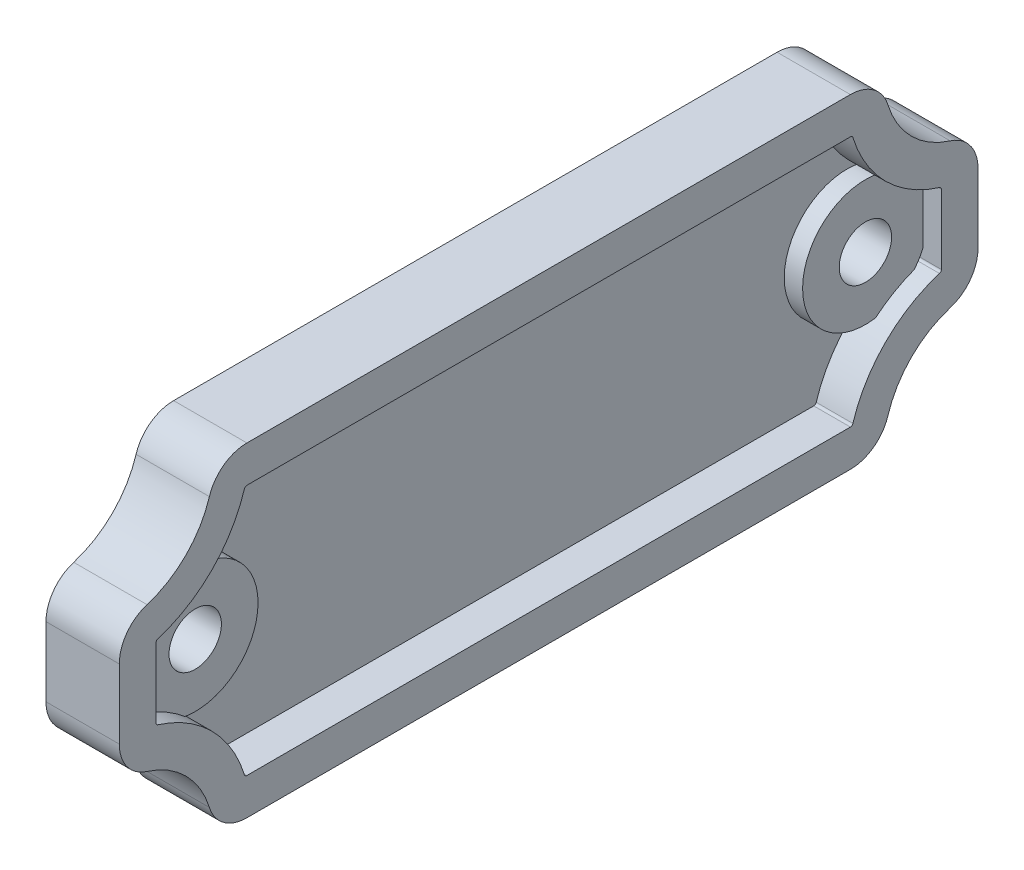
SolidWorks part; units mm, degrees
material "Brass"
ref_plane "Front Plane" through (0, 0, 0) normal (0, 0, 1) x (1, 0, 0)
ref_plane "Top Plane" through (0, 0, 0) normal (0, 1, 0) x (1, 0, 0)
ref_plane "Right Plane" through (0, 0, 0) normal (1, 0, 0) x (0, 0, -1)
sketch "Sketch1" plane through (0, 0, 0) normal (1, 0, 0) x (0, 0, -1)
  line L0 (0, 0) -> (43678.9312, 0) construction
  line L1 (0, 0) -> (0, 43678.9312) construction
  line L2 (-32, 0) -> (-32, 43678.9312) construction
  line L3 (-41, -1031) -> (-41, -15.5) construction
  line L4 (32, 0) -> (32, 43678.9312) construction
  line L5 (41, -1000) -> (41, -15.5) construction
  line L6 (41, 15.5) -> (41, 43678.9312) construction
  line L7 (28.8139, -15.5) -> (-28.8139, -15.5)
  line L8 (41, -3.3139) -> (41, 3.3139)
  line L9 (28.8139, 15.5) -> (-28.8139, 15.5)
  line L10 (-41, -3.3139) -> (-41, 3.3139)
  line L11 (41, -15.5) -> (-41, 15.5) construction
  line L12 (41, 15.5) -> (-41, -15.5) construction
  line L13 (41, -6.5) -> (41, 6.5) construction
  line L14 (-41, -6.5) -> (-41, 6.5) construction
  line L15 (-41, 15.5) -> (-41, 43678.9312) construction
  arc A0 (-32.3981, 12.8529) -> (-38.3529, 6.8981) centre (-41, 15.5) cw
  arc A1 (-32.3981, -12.8529) -> (-38.3529, -6.8981) centre (-41, -15.5) ccw
  arc A2 (32.3981, -12.8529) -> (38.3529, -6.8981) centre (41, -15.5) cw
  arc A3 (32.3981, 12.8529) -> (38.3529, 6.8981) centre (41, 15.5) ccw
  arc A4 (32.3981, 12.8529) -> (28.8139, 15.5) centre (28.8139, 11.75) ccw
  arc A5 (41, 3.3139) -> (38.3529, 6.8981) centre (37.25, 3.3139) ccw
  arc A6 (41, -3.3139) -> (38.3529, -6.8981) centre (37.25, -3.3139) cw
  arc A7 (28.8139, -15.5) -> (32.3981, -12.8529) centre (28.8139, -11.75) ccw
  arc A8 (-32.3981, -12.8529) -> (-28.8139, -15.5) centre (-28.8139, -11.75) ccw
  arc A9 (-38.3529, -6.8981) -> (-41, -3.3139) centre (-37.25, -3.3139) cw
  arc A10 (-41, 3.3139) -> (-38.3529, 6.8981) centre (-37.25, 3.3139) cw
  arc A11 (-32.3981, 12.8529) -> (-28.8139, 15.5) centre (-28.8139, 11.75) cw
  circle A12 centre (-32, 0) radius 2.5
  circle A13 centre (32, 0) radius 2.5
  point P13 (0, 0)
  point P28 (32, 15.5)
  point P37 (32, -15.5)
  point P40 (-32, -15.5)
  point P49 (-32, 15.5)
  dimension "D4" = 9
  dimension "D5" = 3.75
  dimension "D6" = 5
  dimension "D1" = 9
  dimension "D2" = 82
  dimension "D3" = 31
extrude "Boss-Extrude1" add sketch "Sketch1" along normal blind 7
sketch "Sketch6" plane through (7, 0, 0) normal (1, 0, 0) x (0, 0, -1)
  line L8 (28.8139, 12) -> (-28.8139, 12)
  line L9 (-37.5, 3.3139) -> (-37.5, -3.3139)
  line L10 (-28.8139, -12) -> (28.8139, -12)
  line L11 (37.5, -3.3139) -> (37.5, 3.3139)
  line L12 (28.8139, 12) -> (-28.8139, 12)
  line L13 (-37.5, 3.3139) -> (-37.5, -3.3139)
  line L14 (-28.8139, -12) -> (28.8139, -12)
  line L15 (37.5, -3.3139) -> (37.5, 3.3139)
  arc A12 (29.0529, 11.8235) -> (28.8139, 12) centre (28.8139, 11.75) ccw
  arc A13 (29.0529, 11.8235) -> (28.8139, 12) centre (28.8139, 11.75) ccw
  arc A14 (-28.8139, 12) -> (-29.0529, 11.8235) centre (-28.8139, 11.75) ccw
  arc A15 (-28.8139, 12) -> (-29.0529, 11.8235) centre (-28.8139, 11.75) ccw
  arc A16 (-37.3235, 3.5529) -> (-37.5, 3.3139) centre (-37.25, 3.3139) ccw
  arc A17 (-37.3235, 3.5529) -> (-37.5, 3.3139) centre (-37.25, 3.3139) ccw
  arc A18 (-37.5, -3.3139) -> (-37.3235, -3.5529) centre (-37.25, -3.3139) ccw
  arc A19 (-37.5, -3.3139) -> (-37.3235, -3.5529) centre (-37.25, -3.3139) ccw
  arc A20 (-29.0529, -11.8235) -> (-28.8139, -12) centre (-28.8139, -11.75) ccw
  arc A21 (-29.0529, -11.8235) -> (-28.8139, -12) centre (-28.8139, -11.75) ccw
  arc A22 (28.8139, -12) -> (29.0529, -11.8235) centre (28.8139, -11.75) ccw
  arc A23 (28.8139, -12) -> (29.0529, -11.8235) centre (28.8139, -11.75) ccw
  arc A24 (-37.3235, 3.5529) -> (-29.0529, 11.8235) centre (-41, 15.5) ccw
  arc A25 (-29.0529, -11.8235) -> (-37.3235, -3.5529) centre (-41, -15.5) ccw
  arc A26 (37.3235, -3.5529) -> (29.0529, -11.8235) centre (41, -15.5) ccw
  arc A27 (29.0529, 11.8235) -> (37.3235, 3.5529) centre (41, 15.5) ccw
  arc A28 (-37.3235, 3.5529) -> (-29.0529, 11.8235) centre (-41, 15.5) ccw
  arc A29 (-29.0529, -11.8235) -> (-37.3235, -3.5529) centre (-41, -15.5) ccw
  arc A30 (37.3235, -3.5529) -> (29.0529, -11.8235) centre (41, -15.5) ccw
  arc A31 (29.0529, 11.8235) -> (37.3235, 3.5529) centre (41, 15.5) ccw
  arc A32 (37.3235, -3.5529) -> (37.5, -3.3139) centre (37.25, -3.3139) ccw
  arc A33 (37.3235, -3.5529) -> (37.5, -3.3139) centre (37.25, -3.3139) ccw
  arc A34 (37.5, 3.3139) -> (37.3235, 3.5529) centre (37.25, 3.3139) ccw
  arc A35 (37.5, 3.3139) -> (37.3235, 3.5529) centre (37.25, 3.3139) ccw
  dimension "A" = 3.5
extrude "Cut-Extrude1" cut sketch "Sketch6" against normal blind 3.5
sketch "Sketch7" plane through (3.5, 0, 0) normal (1, 0, 0) x (0, 0, -1)
  circle A0 centre (32, 0) radius 6
  circle A1 centre (32, 0) radius 2.5
  dimension "D1" = 12
  dimension "D2" = 5
extrude "Boss-Extrude2" add sketch "Sketch7" along direction (1, 0, 0) on the side against the normal blind 5.25 from offset 0
mirror "Mirror1" about plane through (0, 0, 0) normal (0, 0, 1) of "Boss-Extrude2"
sketch "Sketch8" plane through (3.5, 0, 0) normal (1, 0, 0) x (0, 0, -1)
  circle A0 centre (32, 0) radius 6
  circle A1 centre (32, 0) radius 2.5
  dimension "D1" = 12
  dimension "D2" = 5
extrude "Boss-Extrude3" add sketch "Sketch8" along normal blind 1.75
mirror "Mirror2" about plane through (0, 0, 0) normal (0, 0, 1) of "Boss-Extrude3"
equation "\"A\" = 3.5"
equation "\"B\" = 82"
equation "\"D2@Sketch1\"=\"B\""
equation "\"D1@Boss-Extrude1\"=\"A\"*2"
equation "\"D1@Cut-Extrude1\"=\"A\""
equation "\"D1@Sketch7\"=(\"A\"*2)+5"
equation "\"D1@Boss-Extrude2\"=\"A\"*1.5"
equation "\"D1@Sketch8\"=(\"A\"*2)+5"
equation "\"D1@Boss-Extrude3\"=\"A\"*0.5"
